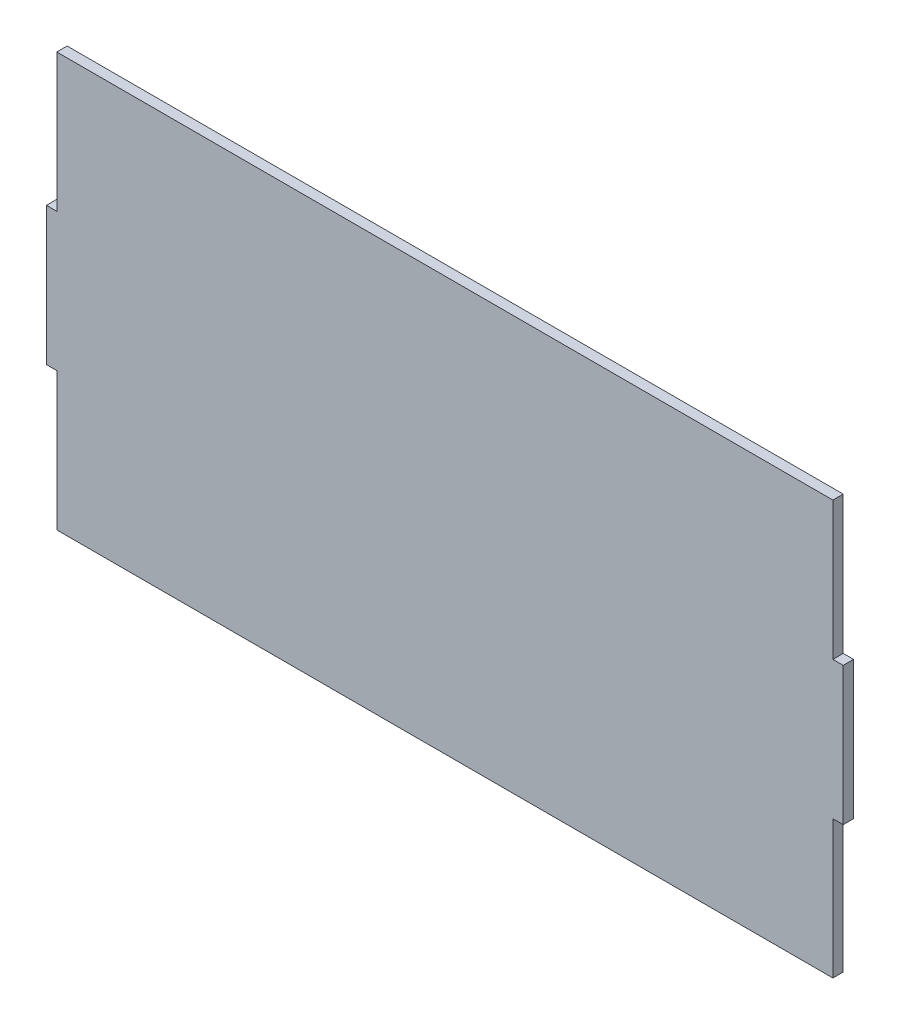
SolidWorks part; units mm, degrees
ref_plane "Front Plane" through (0, 0, 0) normal (0, 0, 1) x (1, 0, 0)
ref_plane "Top Plane" through (0, 0, 0) normal (0, 1, 0) x (1, 0, 0)
ref_plane "Right Plane" through (0, 0, 0) normal (1, 0, 0) x (0, 0, -1)
sketch "Sketch1" plane through (0, 0, 0) normal (0, 0, 1) x (1, 0, 0)
  line L0 (-112.5, 20) -> (-115.5, 20)
  line L1 (-112.5, 60) -> (112.5, 60)
  line L2 (-112.5, 60) -> (-112.5, 20)
  line L3 (-112.5, -60) -> (112.5, -60)
  line L4 (112.5, 60) -> (112.5, 20)
  line L5 (-112.5, 60) -> (112.5, -60) construction
  line L6 (-112.5, -60) -> (112.5, 60) construction
  line L7 (-115.5, 20) -> (-115.5, -20)
  line L8 (-115.5, -20) -> (-112.5, -20)
  line L9 (-112.5, -20) -> (-112.5, -60)
  line L10 (112.5, 20) -> (115.5, 20)
  line L11 (115.5, 20) -> (115.5, -20)
  line L12 (115.5, -20) -> (112.5, -20)
  line L13 (112.5, -20) -> (112.5, -60)
  point P0 (0, 0)
  dimension "D1" = 120
  dimension "D2" = 225
  dimension "D3" = 40
  dimension "D4" = 40
  dimension "D5" = 3
  dimension "D6" = 40
  dimension "D7" = 40
  dimension "D8" = 3
extrude "Boss-Extrude1" add sketch "Sketch1" along normal blind 3
